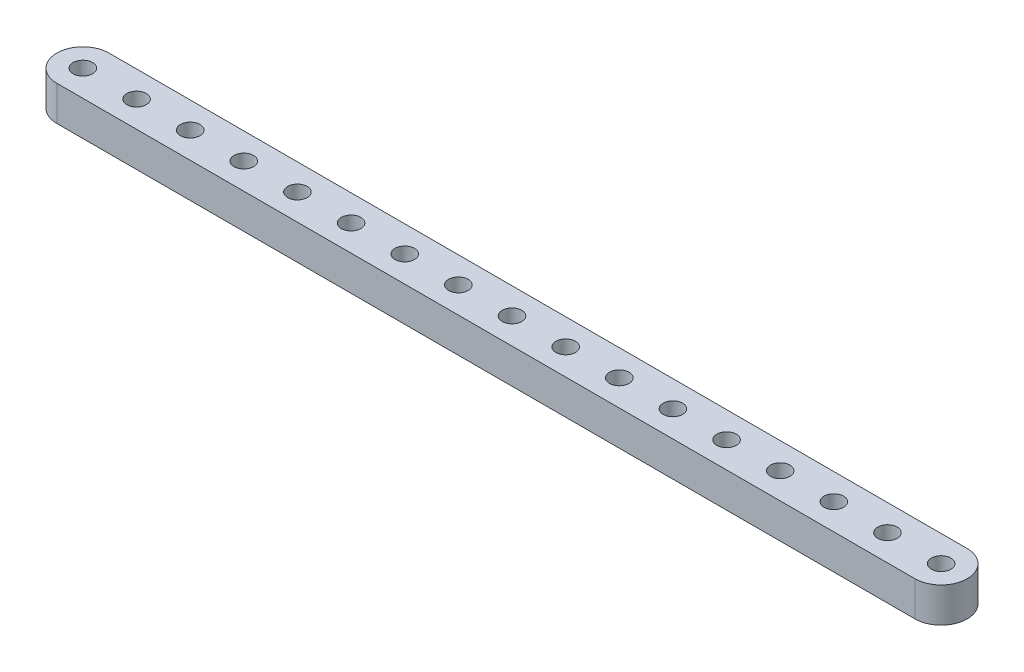
SolidWorks part; units mm, degrees
ref_plane "Front Plane" through (0, 0, 0) normal (0, 0, 1) x (1, 0, 0)
ref_plane "Top Plane" through (0, 0, 0) normal (0, 1, 0) x (1, 0, 0)
ref_plane "Right Plane" through (0, 0, 0) normal (1, 0, 0) x (0, 0, -1)
ref_plane "Plane1" through (0, 6.35, 0) normal (0, 1, 0) x (1, 0, 0)
sketch "Sketch1" plane through (0, 6.35, 0) normal (0, 1, 0) x (1, 0, 0)
  line L0 (78.232, 4.7625) -> (-78.232, 4.7625)
  line L1 (-78.232, -4.7625) -> (78.232, -4.7625)
  arc A0 (78.232, -4.7625) -> (78.232, 4.7625) centre (78.232, 0) ccw
  arc A1 (-78.232, 4.7625) -> (-78.232, -4.7625) centre (-78.232, 0) ccw
  circle A2 centre (78.232, 0) radius 1.778
  circle A3 centre (68.453, 0) radius 1.778
  circle A4 centre (58.674, 0) radius 1.778
  circle A5 centre (48.895, 0) radius 1.778
  circle A6 centre (39.116, 0) radius 1.778
  circle A7 centre (29.337, 0) radius 1.778
  circle A8 centre (19.558, 0) radius 1.778
  circle A9 centre (9.779, 0) radius 1.778
  circle A10 centre (0, 0) radius 1.778
  circle A11 centre (-9.779, 0) radius 1.778
  circle A12 centre (-19.558, 0) radius 1.778
  circle A13 centre (-29.337, 0) radius 1.778
  circle A14 centre (-39.116, 0) radius 1.778
  circle A15 centre (-48.895, 0) radius 1.778
  circle A16 centre (-58.674, 0) radius 1.778
  circle A17 centre (-68.453, 0) radius 1.778
  circle A18 centre (-78.232, 0) radius 1.778
extrude "Boss-Extrude1" add sketch "Sketch1" against normal blind 6.35
